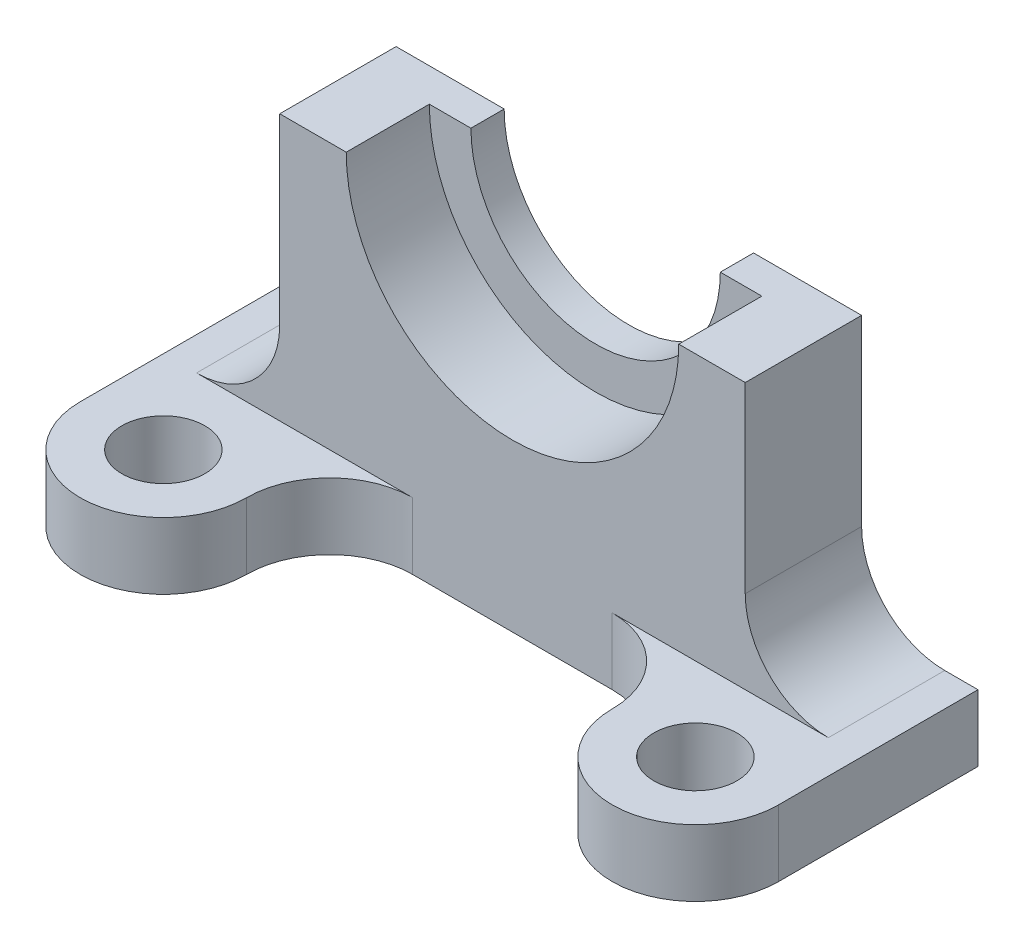
SolidWorks part; units mm, degrees
ref_plane "Front Plane" through (0, 0, 0) normal (0, 0, 1) x (1, 0, 0)
ref_plane "Top Plane" through (0, 0, 0) normal (0, 1, 0) x (1, 0, 0)
ref_plane "Right Plane" through (0, 0, 0) normal (1, 0, 0) x (0, 0, -1)
sketch "Sketch2" plane through (0, 0, 0) normal (0, 1, 0) x (1, 0, 0)
  line L0 (0, 0) -> (0, -44.45) construction
  line L1 (-133.35, 0) -> (133.35, 0)
  line L2 (133.35, -76.2) -> (133.35, 0)
  line L3 (-133.35, -76.2) -> (-133.35, 0)
  line L7 (-38.1, -44.45) -> (38.1, -44.45)
  circle A0 centre (101.6, -76.2) radius 15.875
  arc A1 (69.85, -76.2) -> (133.35, -76.2) centre (101.6, -76.2) ccw
  arc A2 (69.85, -76.2) -> (38.1, -44.45) centre (38.1, -76.2) ccw
  arc A3 (-69.85, -76.2) -> (-38.1, -44.45) centre (-38.1, -76.2) cw
  arc A4 (-69.85, -76.2) -> (-133.35, -76.2) centre (-101.6, -76.2) cw
  circle A5 centre (-101.6, -76.2) radius 15.875
  dimension "D3" = 31.75
  dimension "D2" = 15.875
  dimension "D5" = 44.45
  dimension "D7" = 31.75
  dimension "D1" = 76.2
  dimension "D10" = 101.6
  dimension "D6" = 76.2
  dimension "D8" = 133.35
  dimension "D9" = 38.1
extrude "Boss-Extrude1" add sketch "Sketch2" along normal blind 25.4
sketch "Sketch3" plane through (0, 0, 0) normal (0, 0, -1) x (-1, 0, 0)
  line L0 (0, 25.4) -> (0, 127) construction
  line L1 (-133.35, 25.4) -> (133.35, 25.4) construction
  line L2 (-63.5, 127) -> (-88.9, 127)
  line L3 (-88.9, 127) -> (-88.9, 57.15)
  line L4 (120.65, 25.4) -> (0, 25.4)
  line L8 (-133.35, 0) -> (133.35, 0) construction
  line L9 (0, 127) -> (0, 0) construction
  line L13 (88.9, 127) -> (88.9, 57.15)
  line L14 (63.5, 127) -> (88.9, 127)
  line L15 (-120.65, 25.4) -> (0, 25.4)
  arc A0 (-63.5, 127) -> (63.5, 127) centre (0, 127) ccw
  arc A1 (-120.65, 25.4) -> (-88.9, 57.15) centre (-120.65, 57.15) ccw
  arc A2 (120.65, 25.4) -> (88.9, 57.15) centre (120.65, 57.15) cw
  dimension "D2" = 63.5
  dimension "D4" = 31.75
  dimension "D1" = 101.6
  dimension "D3" = 88.9
extrude "Boss-Extrude2" add sketch "Sketch3" against normal blind 44.45
sketch "Sketch4" plane through (0, 0, 0) normal (0, 0, -1) x (-1, 0, 0)
  line L0 (-133.35, 0) -> (133.35, 0) construction
  line L1 (-63.5, 127) -> (63.5, 127)
  arc A0 (-47.625, 127) -> (47.625, 127) centre (0, 127) ccw
  arc A1 (-63.5, 127) -> (63.5, 127) centre (0, 127) ccw
  arc M7 (63.5, 127) -> (-63.5, 127) centre (0, 127) cw
  dimension "D2" = 95.25
  dimension "D1" = 127
  dimension "D3" = 127
extrude "Boss-Extrude3" add sketch "Sketch4" against normal blind 12.7 contours A0 L1 M7
